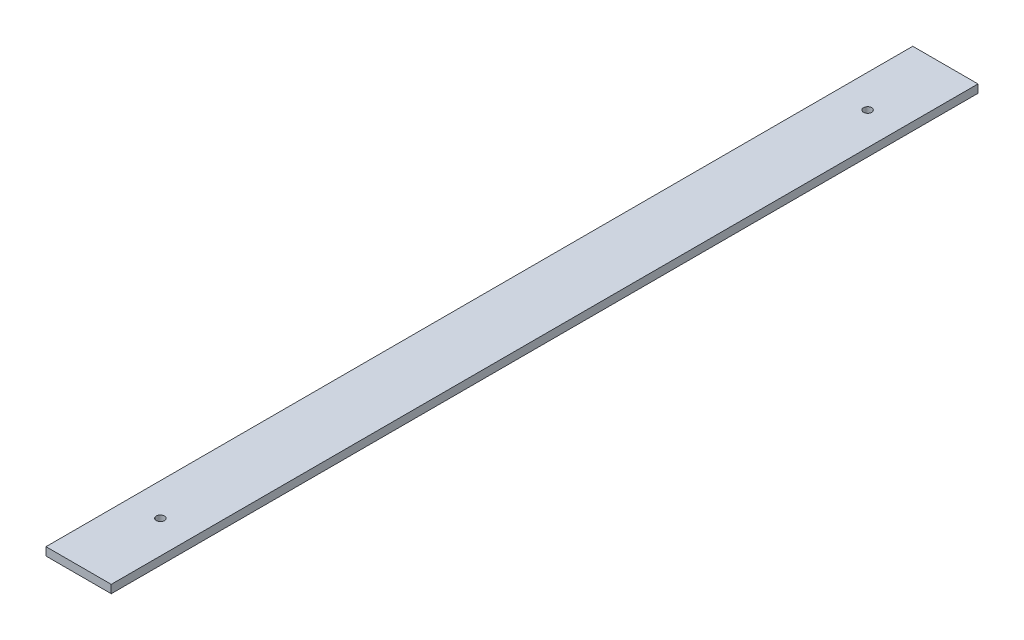
SolidWorks part; units mm, degrees
material "6063-O"
ref_plane "Front Plane" through (0, 0, 0) normal (0, 0, 1) x (1, 0, 0)
ref_plane "Top Plane" through (0, 0, 0) normal (0, 1, 0) x (1, 0, 0)
ref_plane "Right Plane" through (0, 0, 0) normal (1, 0, 0) x (0, 0, -1)
sketch "Sketch4" plane through (0, 0, 0) normal (0, 1, 0) x (1, 0, 0)
  line L4 (23232.9446, -10111.0305) -> (23232.9446, -10251.0305) construction
  line L5 (23232.9446, -9942.5829) -> (23032.9446, -9942.5829)
  line L6 (23232.9446, -9942.5829) -> (23232.9446, -12876.1567)
  line L7 (23232.9446, -12876.1567) -> (23032.9446, -12876.1567)
  line L8 (23032.9446, -9942.5829) -> (23032.9446, -12876.1567)
  line L9 (22132.9446, -9942.5829) -> (21932.9446, -9942.5829)
  line L10 (22132.9446, -9942.5829) -> (22132.9446, -12833.5838)
  line L11 (22132.9446, -12833.5838) -> (21932.9446, -12833.5838)
  line L12 (21932.9446, -9942.5829) -> (21932.9446, -12833.5838)
  line L13 (20932.9446, -9942.5829) -> (20732.9446, -9942.5829)
  line L14 (20932.9446, -9942.5829) -> (20932.9446, -12599.4325)
  line L15 (20932.9446, -12599.4325) -> (20732.9446, -12599.4325)
  line L16 (20732.9446, -9942.5829) -> (20732.9446, -12599.4325)
  line L17 (19732.9446, -9942.5829) -> (19532.9446, -9942.5829)
  line L18 (19732.9446, -9942.5829) -> (19732.9446, -12109.8436)
  line L19 (19732.9446, -12109.8436) -> (19532.9446, -12109.8436)
  line L20 (19532.9446, -9942.5829) -> (19532.9446, -12109.8436)
  line L21 (18902.9446, -9942.5829) -> (18702.9446, -9942.5829)
  line L22 (18902.9446, -9942.5829) -> (18902.9446, -11636.2195)
  line L23 (18902.9446, -11636.2195) -> (18702.9446, -11636.2195)
  line L24 (18702.9446, -9942.5829) -> (18702.9446, -11636.2195)
  line L25 (18702.9446, -10111.0305) -> (18702.9446, -10251.0305) construction
  line L26 (23132.9446, -12748.1199) -> (23132.9446, -12608.0593) construction
  line L27 (22032.9446, -12550.6075) -> (22032.9446, -12691.8491) construction
  line L28 (20832.9446, -12422.3488) -> (20832.9446, -12275.1597) construction
  line L29 (19632.9446, -11906.9658) -> (19632.9446, -11746.8651) construction
  line L30 (18802.9446, -11371.765) -> (18802.9446, -11195.5746) construction
  line L31 (23132.9446, -10251.0305) -> (23132.9446, -10111.0305) construction
  line L32 (18702.9446, -10251.0305) -> (23232.9446, -10251.0305) construction
  line L33 (23232.9446, -10111.0305) -> (18702.9446, -10111.0305) construction
  circle A0 centre (23132.9446, -12678.0896) radius 12.5
  arc A1 (18702.9446, -11295.1434) -> (23232.9446, -12744.4799) centre (22932.9446, -5878.0705) ccw construction
  arc A2 (18702.9446, -11116.3765) -> (23232.9446, -12604.3436) centre (22932.9446, -5878.0705) ccw construction
  circle A3 centre (22032.9446, -12621.2283) radius 12.5
  circle A4 centre (20832.9446, -12348.7542) radius 12.5
  circle A5 centre (19632.9446, -11826.9154) radius 12.5
  circle A6 centre (18802.9446, -11283.6698) radius 12.5
  circle A7 centre (18802.9446, -10181.0305) radius 12.5
  circle A8 centre (19632.9446, -10181.0305) radius 12.5
  circle A9 centre (20832.9446, -10181.0305) radius 12.5
  circle A10 centre (22032.9446, -10181.0305) radius 12.5
  circle A11 centre (23132.9446, -10181.0305) radius 12.5
  arc A12 (18702.9446, -11116.3765) -> (23232.9446, -12604.3436) centre (22932.9446, -5878.0705) ccw construction
  point P22 (23132.9446, -9942.5829)
  point P23 (22032.9446, -9942.5829)
  point P24 (20832.9446, -9942.5829)
  point P25 (19632.9446, -9942.5829)
  point P26 (23132.9446, -12876.1567)
  point P30 (20832.9446, -12599.4325)
  point P40 (23132.9446, -12678.0896)
  point P59 (22032.9446, -12621.2283)
  point P60 (22032.9446, -12833.5838)
  point P68 (20832.9446, -12348.7542)
  point P69 (19632.9446, -12109.8436)
  point P73 (19632.9446, -11826.9154)
  point P74 (18802.9446, -11283.6698)
  point P75 (18802.9446, -11636.2195)
  point P78 (23132.9446, -10181.0305)
  point P91 (18802.9446, -9942.5829)
  dimension "D5" = 25
  dimension "D1" = 200
  dimension "D2" = 1200
  dimension "D3" = 1200
  dimension "D4" = 1200
  dimension "D6" = 100
  dimension "D7" = 70
extrude "Boss-Extrude1" add sketch "Sketch4" along normal blind 25
sketch "Sketch5" plane through (0, 0, 0) normal (0, 1, 0) x (1, 0, 0)
  line L1 (21672.9496, -13744.6988) -> (23911.3404, -13744.6988)
  line L2 (21672.9496, -13744.6988) -> (21672.9496, -8510.0369)
  line L3 (21672.9496, -8510.0369) -> (23911.3404, -8510.0369)
  line L4 (23911.3404, -13744.6988) -> (23911.3404, -8510.0369)
  line L5 (20104.3136, -9003.5403) -> (17654.4213, -9003.5403)
  line L6 (20104.3136, -9003.5403) -> (20104.3136, -13956.2003)
  line L7 (20104.3136, -13956.2003) -> (17654.4213, -13956.2003)
  line L8 (17654.4213, -9003.5403) -> (17654.4213, -13956.2003)
extrude "Cut-Extrude1" cut sketch "Sketch5" along normal through all
